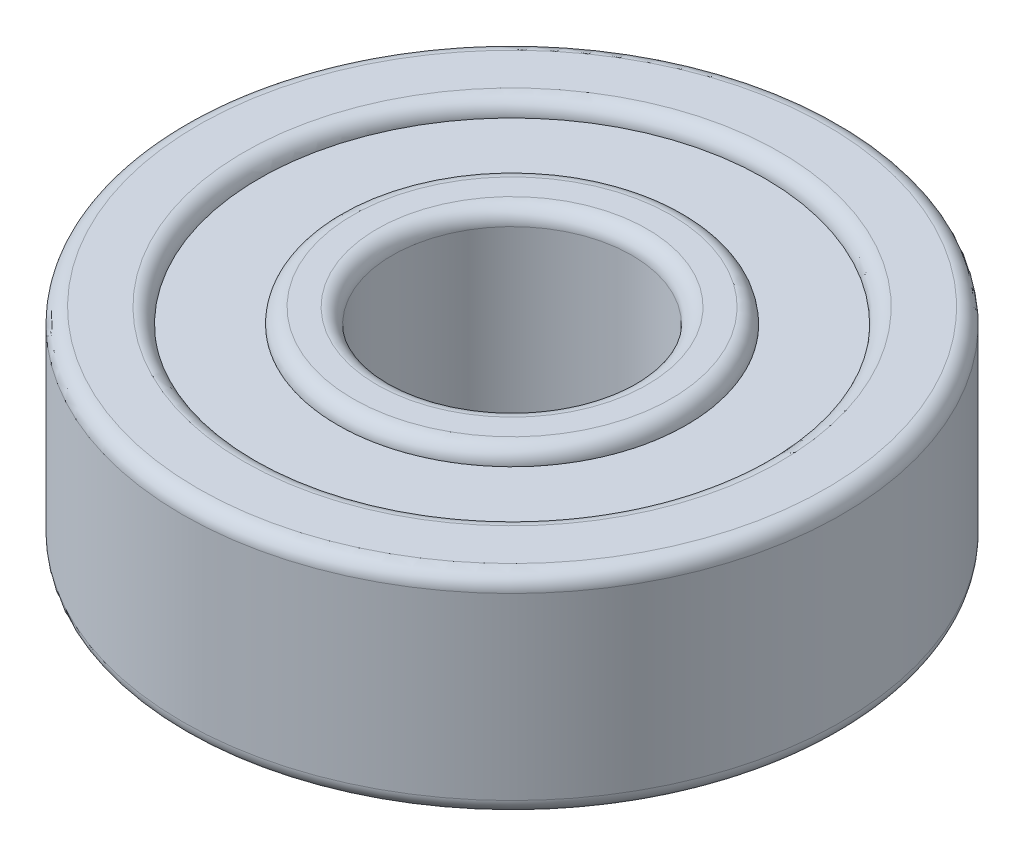
SolidWorks part; units mm, degrees
material "Alloy Steel"
ref_plane "Front" through (0, 0, 0) normal (0, 0, 1) x (1, 0, 0)
ref_plane "Top" through (0, 0, 0) normal (0, 1, 0) x (1, 0, 0)
ref_plane "Right" through (0, 0, 0) normal (1, 0, 0) x (0, 0, -1)
sketch "Sketch1" plane through (0, 0, 0) normal (0, 1, 0) x (1, 0, 0)
  circle A0 centre (0, 0) radius 11
  circle A1 centre (0, 0) radius 4
  dimension "D1" = 22
  dimension "D2" = 8
extrude "Boss-Extrude1" add sketch "Sketch1" along normal mid plane 7
sketch "Sketch2" plane through (0, 3.5, 0) normal (0, 1, 0) x (1, 0, 0)
  circle A0 centre (0, 0) radius 8.44
  circle A1 centre (0, 0) radius 5.82
  dimension "D1" = 11.64
  dimension "D2" = 16.88
extrude "Cut-Extrude1" cut sketch "Sketch2" against normal through all
sketch "Sketch3" plane through (0, 0, 0) normal (1, 0, 0) x (0, 0, -1)
  line L0 (-11, 0) -> (11, 0) construction
  line L1 (-11, 3.5) -> (-11, -3.5) construction
  line L2 (11, -3.5) -> (11, 3.5) construction
  line L3 (4, 8.4686) -> (4, -1.7841) construction
  line L4 (11, 8.4686) -> (11, -1.7841) construction
  line L5 (11, -3.5) -> (11, 3.5) construction
  line L7 (0, 8.4686) -> (0, -1.7841) construction
  circle A0 centre (7.27, 0) radius 2.33
  dimension "D2" = 4.66
  dimension "D1" = 3.27
revolve "Cut-Revolve1" cut sketch "Sketch3" angle 360 about L7
fillet "Fillet1" radius 0.508 4 edges at (0, -3.5, 8.44) (0, 3.5, 8.44) (0, -3.5, 11) (0, 3.5, 11)
fillet "Fillet2" radius 0.508 4 edges at (0, -3.5, 4) (0, -3.5, 5.82) (0, 3.5, 4) (0, 3.5, 5.82)
sketch "Sketch4" plane through (0, 0, 0) normal (1, 0, 0) x (0, 0, -1)
  line L0 (7.27, 2.33) -> (7.27, -2.33)
  line L1 (7.27, 8.5081) -> (7.27, -1.5343) construction
  arc A0 (5.82, 1.8239) -> (5.82, -1.8239) centre (7.27, 0) ccw construction
  arc A1 (7.27, 2.33) -> (7.27, -2.33) centre (7.27, 0) cw
  arc A3 (5.82, 1.8239) -> (5.82, -1.8239) centre (7.27, 0) ccw construction
revolve "Revolve1" add sketch "Sketch4" angle 360 about L1
pattern_circular "CirPattern2" count 7 over 360 about axis through (0, 0, 0) along (0, 1, 0) of bodies 106
ref_plane "Plane1" through (0, 2.015, 0) normal (0, -1, 0) x (1, 0, 0)
ref_plane "Plane2" through (0, 2.992, 0) normal (0, -1, 0) x (1, 0, 0)
sketch "Sketch5" plane through (0, 0, 0) normal (0, 1, 0) x (1, 0, 0)
  circle A0 centre (0, 0) radius 5.82 construction
  circle A1 centre (0, 0) radius 8.44 construction
  circle A2 centre (0, 0) radius 5.82
  circle A3 centre (0, 0) radius 8.44
extrude "Boss-Extrude4" add sketch "Sketch5" along normal up to surface (0.9771 mm away) from surface at 2.0149 separate body up to plane "Plane2" starting at plane "Plane1"
mirror "Mirror1" about plane through (0, 0, 0) normal (0, 1, 0) of bodies 113
